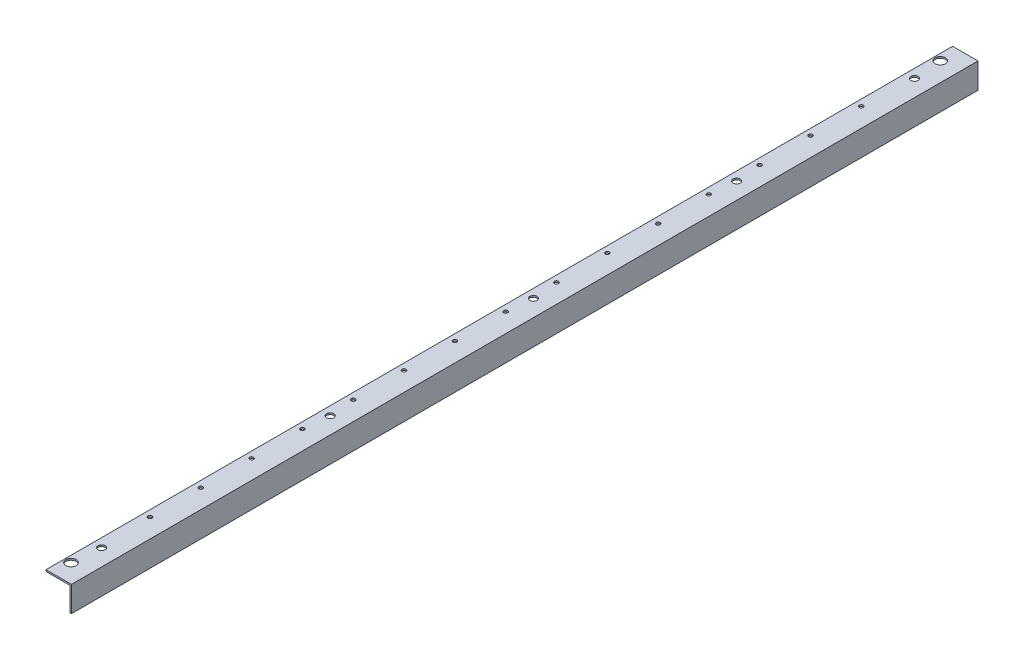
SolidWorks part; units mm, degrees
material "6063-T6"
ref_plane "Front Plane" through (0, 0, 0) normal (0, 0, 1) x (1, 0, 0)
ref_plane "Top Plane" through (0, 0, 0) normal (0, 1, 0) x (1, 0, 0)
ref_plane "Right Plane" through (0, 0, 0) normal (1, 0, 0) x (0, 0, -1)
sketch "Sketch1" plane through (0, 0, 0) normal (0, 0, 1) x (1, 0, 0)
  line L0 (0, 0) -> (-50.8, 0)
  line L1 (-50.8, 0) -> (-50.8, -3.175)
  line L2 (-50.8, -3.175) -> (-3.175, -3.175)
  line L3 (-3.175, -3.175) -> (-3.175, -50.8)
  line L4 (-3.175, -50.8) -> (0, -50.8)
  line L5 (0, -50.8) -> (0, 0)
  dimension "D1" = 50.8
  dimension "D2" = 3.175
extrude "Boss-Extrude1" add sketch "Sketch1" along normal blind 1812.925
sketch "Sketch2" plane through (0, 0, 0) normal (0, 1, 0) x (1, 0, 0)
  line L0 (0, 0) -> (-50.8, 0) construction
  line L1 (0, -1812.925) -> (0, 0) construction
  circle A0 centre (-38.1, -37.3063) radius 10.3188
  circle A1 centre (-38.1, -1775.6188) radius 10.3187
  circle A2 centre (-33.3375, -93.6625) radius 7.1438
  circle A3 centre (-33.3375, -449.2625) radius 7.1438
  circle A4 centre (-33.3375, -855.6625) radius 7.1437
  circle A5 centre (-33.3375, -1262.0625) radius 7.1438
  circle A6 centre (-33.3375, -1719.2625) radius 7.1438
  dimension "D1" = 20.6375
  dimension "D2" = 14.2875
  dimension "D3" = 37.3062
  dimension "D4" = 38.1
  dimension "D5" = 1775.6188
  dimension "D6" = 33.3375
  dimension "D7" = 93.6625
  dimension "D8" = 449.2625
  dimension "D9" = 855.6625
  dimension "D10" = 1262.0625
  dimension "D11" = 1719.2625
extrude "Cut-Extrude1" cut sketch "Sketch2" against normal through all
extrude "Cut-Extrude3" cut sketch "Sketch4" against normal blind 44.45
sketch "Sketch4" plane through (-2.0299, 0, 893.1633) normal (0, 1, 0) x (1, 0, 0)
  circle A0 centre (-36.0701, 697.9008) radius 3.9687
pattern_linear "LPattern1" count 15 spacing 101.6 along (0, 0, 1) of "Cut-Extrude3"
